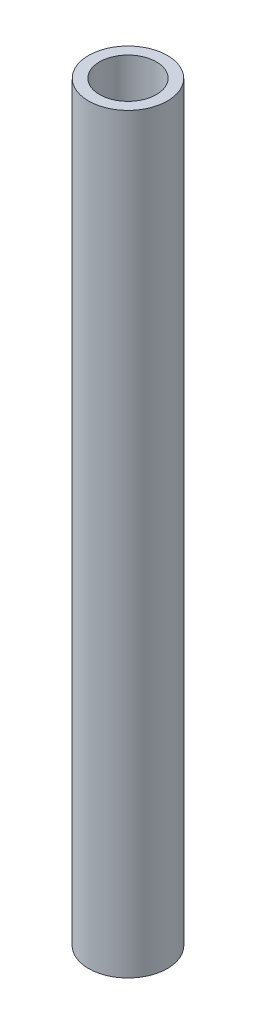
SolidWorks part; units mm, degrees
material "AISI 316 Stainless Steel Sheet (SS)"
ref_plane "Front Plane" through (0, 0, 0) normal (0, 0, 1) x (1, 0, 0)
ref_plane "Top Plane" through (0, 0, 0) normal (0, 1, 0) x (1, 0, 0)
ref_plane "Right Plane" through (0, 0, 0) normal (1, 0, 0) x (0, 0, -1)
sketch "Sketch1" plane through (0, 0, 0) normal (0, 1, 0) x (1, 0, 0)
  circle A0 centre (0, 0) radius 3.175
  circle A1 centre (0, 0) radius 2.286
  dimension "D1" = 6.35
  dimension "D2" = 4.572
extrude "Boss-Extrude1" add sketch "Sketch1" along normal blind 60.4807
